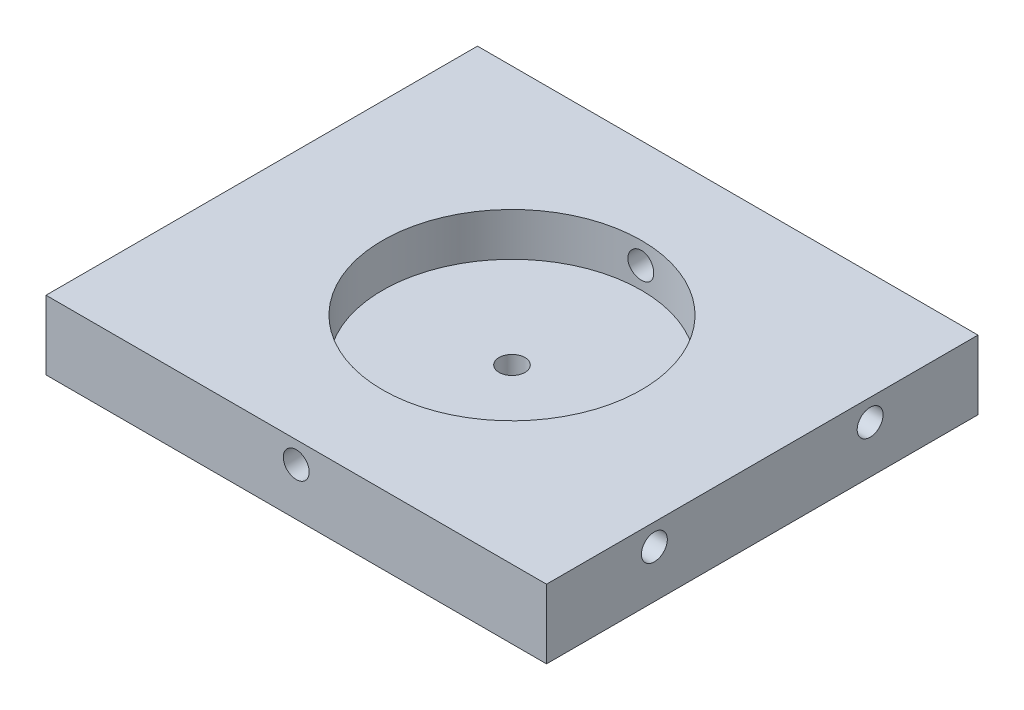
SolidWorks part; units mm, degrees
ref_plane "Plan de face" through (0, 0, 0) normal (0, 0, 1) x (1, 0, 0)
ref_plane "Plan de dessus" through (0, 0, 0) normal (0, 1, 0) x (1, 0, 0)
ref_plane "Plan de droite" through (0, 0, 0) normal (1, 0, 0) x (0, 0, -1)
sketch "Esquisse1" plane through (0, 0, 0) normal (0, 0, 1) x (1, 0, 0)
  line L0 (-5.5, -49) -> (52.5, -49) construction
  line L5 (-5.5, -45) -> (52.5, -45)
  line L6 (-5.5, -45) -> (-5.5, -53)
  line L7 (-5.5, -53) -> (52.5, -53)
  line L8 (52.5, -45) -> (52.5, -53)
  line L9 (23.5, -45) -> (23.5, -53) construction
  dimension "D1" = 8
  dimension "D2" = 58
extrude "Boss.-Extru.1" add sketch "Esquisse1" along normal blind 50
sketch "Esquisse2" plane through (0, -45, 0) normal (0, 1, 0) x (-1, 0, 0)
  line L0 (5.5, 50) -> (-52.5, 50) construction
  line L7 (-52.5, 50) -> (-52.5, 0) construction
  circle A0 centre (-23.5, 25) radius 15
  dimension "D10" = 29
  dimension "D11" = 25
extrude "Enlèv. mat.-Extru.1" cut sketch "Esquisse2" against normal blind 5
sketch "Esquisse3" plane through (-5.5, 0, 0) normal (-1, 0, 0) x (0, 0, 1)
  line L0 (50, -53) -> (0, -53) construction
  line L1 (0, -45) -> (0, -53) construction
  line L2 (50, -45) -> (50, -53) construction
  circle A0 centre (12.5, -47.5) radius 1.5
  circle A1 centre (37.5, -47.5) radius 1.5
  dimension "D1" = 5.5
  dimension "D2" = 5.5
  dimension "D3" = 12.5
  dimension "D4" = 12.5
extrude "Enlèv. mat.-Extru.2" cut sketch "Esquisse3" against normal blind 10
sketch "Esquisse4" plane through (52.5, 0, 0) normal (1, 0, 0) x (0, 0, -1)
  line L0 (-50, -53) -> (0, -53) construction
  line L1 (-50, -45) -> (-50, -53) construction
  line L2 (0, -45) -> (0, -53) construction
  circle A0 centre (-37.5, -47.5) radius 1.5
  circle A1 centre (-12.5, -47.5) radius 1.5
  dimension "D1" = 5.5
  dimension "D2" = 5.5
  dimension "D3" = 12.5
  dimension "D4" = 12.5
extrude "Enlèv. mat.-Extru.3" cut sketch "Esquisse4" against normal blind 10
sketch "Esquisse5" plane through (0, -50, 0) normal (0, 1, 0) x (1, 0, 0)
  line L0 (-5.5, 0) -> (52.5, -50) construction
  line L1 (-5.5, -50) -> (52.5, 0) construction
  circle A1 centre (23.5, -25) radius 1.5
extrude "Enlèv. mat.-Extru.4" cut sketch "Esquisse5" against normal through all
sketch "Esquisse6" plane through (0, 0, 0) normal (0, 0, -1) x (-1, 0, 0)
  line L0 (5.5, -45) -> (-52.5, -45) construction
  line L1 (5.5, -45) -> (5.5, -53) construction
  circle A0 centre (-23.5, -47.5) radius 1.5
  dimension "D1" = 2.5
  dimension "D2" = 29
extrude "Enlèv. mat.-Extru.5" cut sketch "Esquisse6" against normal through all
